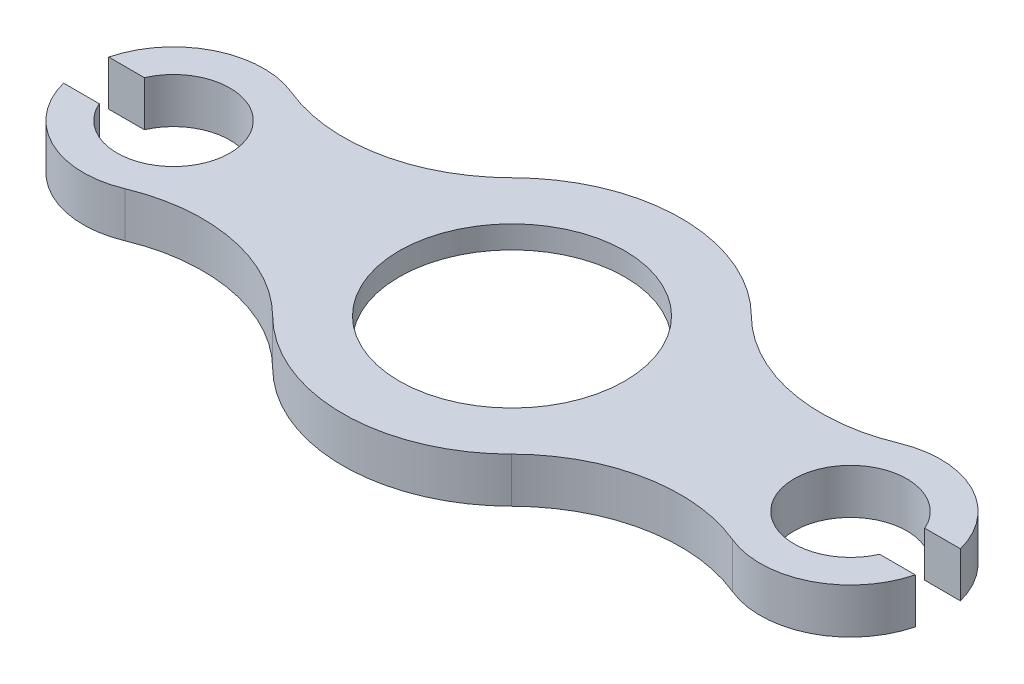
SolidWorks part; units mm, degrees
ref_plane "Front Plane" through (0, 0, 0) normal (0, 0, 1) x (1, 0, 0)
ref_plane "Top Plane" through (0, 0, 0) normal (0, 1, 0) x (1, 0, 0)
ref_plane "Right Plane" through (0, 0, 0) normal (1, 0, 0) x (0, 0, -1)
sketch "Sketch1" plane through (0, 0, 0) normal (0, 1, 0) x (1, 0, 0)
  line L0 (-132.6923, -1359.0664) -> (-132.6923, -197.6) construction
  line L1 (17.3077, 49.7976) -> (17.3077, -122.0648) construction
  line L2 (167.3077, -41.07) -> (167.3077, -76.1336) construction
  line L3 (1267.3077, -36.1336) -> (242.975, -36.1336) construction
  line L4 (-132.6923, -63.229) -> (-132.6923, -36.1336) construction
  line L5 (-92.6923, -36.1336) -> (-132.6923, -36.1336) construction
  line L6 (-132.6923, -36.1336) -> (-172.6923, -36.1336) construction
  line L7 (127.3077, -36.1336) -> (92.3077, -36.1336) construction
  line L8 (92.3077, -36.1336) -> (-92.6923, -36.1336) construction
  line L9 (-207.0378, -36.1336) -> (-1227.3348, -36.1336) construction
  line L10 (-171.4221, -46.1336) -> (-155.6052, -46.1336)
  line L12 (-171.4221, -26.1336) -> (-155.6052, -26.1336)
  line L14 (207.3077, -36.1336) -> (127.3077, -36.1336) construction
  line L16 (190.2206, -26.1336) -> (206.0375, -26.1336)
  line L18 (190.2206, -46.1336) -> (206.0375, -46.1336)
  line L21 (207.3077, -36.1336) -> (214.3728, -34.1528) construction
  line L22 (-132.6923, -11.1336) -> (-132.6923, 3.8664) construction
  arc A0 (-117.359, 0.8108) -> (-171.4221, -26.1336) centre (-132.6923, -36.1336) ccw
  arc A1 (127.3077, -36.1336) -> (206.0375, -46.1336) centre (167.3077, -36.1336) ccw
  circle A2 centre (17.3077, -36.1336) radius 50
  circle A3 centre (17.3077, -36.1336) radius 67.75
  circle A4 centre (17.3077, -36.1336) radius 75
  arc A5 (-117.359, 0.8108) -> (-35.6506, 16.974) centre (-88.609, 70.0816) ccw
  arc A6 (-35.6506, -89.2412) -> (-117.359, -73.078) centre (-88.609, -142.3488) ccw
  arc A7 (151.9744, -73.078) -> (70.266, -89.2412) centre (123.2244, -142.3488) ccw
  arc A8 (70.266, 16.974) -> (151.9744, 0.8108) centre (123.2244, 70.0816) ccw
  arc A9 (-92.6923, -36.1336) -> (-117.359, 0.8108) centre (-132.6923, -36.1336) ccw construction
  arc A10 (-117.359, -73.078) -> (-92.6923, -36.1336) centre (-132.6923, -36.1336) ccw construction
  arc A11 (151.9744, 0.8108) -> (127.3077, -36.1336) centre (167.3077, -36.1336) ccw construction
  arc A12 (-155.6052, -46.1336) -> (-155.6052, -26.1336) centre (-132.6923, -36.1336) ccw
  arc A13 (190.2206, -26.1336) -> (190.2206, -46.1336) centre (167.3077, -36.1336) ccw
  arc A14 (-171.4221, -46.1336) -> (-117.359, -73.078) centre (-132.6923, -36.1336) ccw
  arc A15 (206.0375, -26.1336) -> (151.9744, 0.8108) centre (167.3077, -36.1336) ccw
  point P33 (-172.6923, -36.1336)
  point P38 (207.3077, -36.1336)
  dimension "D3" = 80
  dimension "D4" = 80
  dimension "D5" = 100
  dimension "D6" = 135.5
  dimension "D7" = 150
  dimension "D8" = 150
  dimension "D9" = 150
  dimension "D10" = 150
  dimension "D11" = 150
  dimension "D12" = 50
  dimension "D2" = 50
  dimension "D1" = 150
extrude "Boss-Extrude1" add sketch "Sketch1" along normal blind 20
sketch "Sketch2" plane through (0, 20, 0) normal (0, 1, 0) x (1, 0, 0)
  line L0 (-132.6923, 35.9298) -> (-132.6923, -151.7817) construction
  line L1 (17.3077, 51.2835) -> (17.3077, -169.6118) construction
  line L2 (167.3077, 51.2835) -> (167.3077, -169.6118) construction
  line L3 (-231.0757, -36.1336) -> (240.4318, -36.1336) construction
  arc A0 (-155.6052, -46.1336) -> (-155.6052, -26.1336) centre (-132.6923, -36.1336) ccw construction
  arc A1 (190.2206, -26.1336) -> (190.2206, -46.1336) centre (167.3077, -36.1336) ccw construction
  circle A4 centre (17.3077, -36.1336) radius 50
  dimension "D3" = 100
  dimension "D1" = 150
  dimension "D2" = 150
extrude "Cut-Extrude1" cut sketch "Sketch2" against normal through all
sketch "Sketch3" plane through (0, 0, 0) normal (0, -1, 0) x (1, 0, 0)
  line L0 (-132.5148, 97.5109) -> (-132.5148, -82.2761)
  line L1 (17.4852, 135.1523) -> (17.4852, -76.828)
  line L2 (167.4852, 138.6192) -> (167.4852, -96.6392)
  line L3 (-193.9296, 36.1336) -> (247.3657, 36.1336)
  arc A0 (-155.6052, 26.1336) -> (-155.6052, 46.1336) centre (-132.6923, 36.1336) ccw construction
  circle A1 centre (17.3077, 36.1336) radius 50 construction
  arc A3 (190.2206, 46.1336) -> (190.2206, 26.1336) centre (167.3077, 36.1336) ccw construction
  arc A4 (190.2206, 46.1336) -> (190.2206, 26.1336) centre (167.3077, 36.1336) ccw
  circle A5 centre (17.3077, 36.1336) radius 67.8
  dimension "D3" = 135.6
  dimension "D1" = 150
  dimension "D2" = 150
extrude "Cut-Extrude2" cut sketch "Sketch3" against normal blind 10 contours A5
